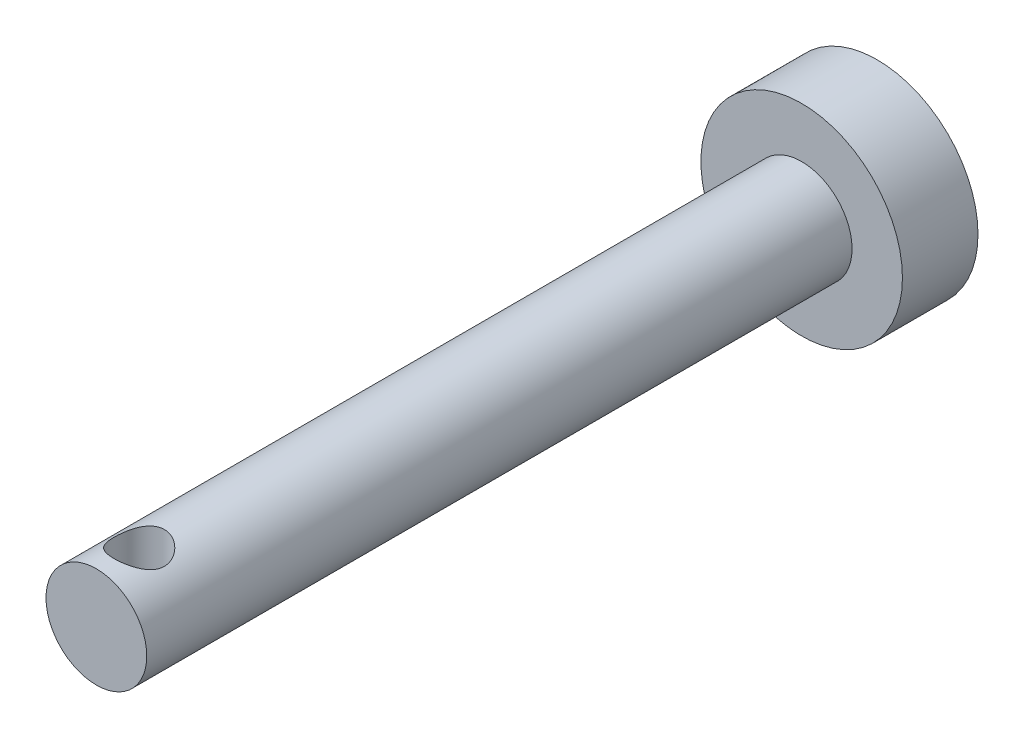
SolidWorks part; units mm, degrees
ref_plane "Front Plane" through (0, 0, 0) normal (0, 0, 1) x (1, 0, 0)
ref_plane "Top Plane" through (0, 0, 0) normal (0, 1, 0) x (1, 0, 0)
ref_plane "Right Plane" through (0, 0, 0) normal (1, 0, 0) x (0, 0, -1)
sketch "Sketch1" plane through (0, 0, 0) normal (1, 0, 0) x (0, 0, -1)
  line L0 (-125, 0) -> (125, 0) construction
  line L1 (125, 4) -> (125, -4) construction
  line L2 (125, 4) -> (122, 4) construction
  line L3 (-125, -2) -> (-125, 2) construction
  point P7 (-125, 0)
  dimension "Length" = 250
  dimension "Head Height" = 3
  dimension "Head Diameter" = 8
  dimension "Diameter" = 4
sketch "Sketch2" plane through (0, 0, 0) normal (1, 0, 0) x (0, 0, -1)
  line L0 (125, 0) -> (125, 4)
  line L1 (125, 4) -> (122, 4)
  line L2 (122, 4) -> (122, 2)
  line L3 (122, 2) -> (-125, 2)
  line L4 (-125, 2) -> (-125, 0)
  line L5 (-125, 0) -> (125, 0)
revolve "Revolve1" add sketch "Sketch2" angle 360 about L0
sketch "Sketch3" plane through (0, 0, 0) normal (1, 0, 0) x (0, 0, -1)
  line L0 (122, 4) -> (122, -4) construction
  line L1 (94, 4.0673) -> (-206, 4.0673)
  line L2 (94, 4.0673) -> (94, -3.766)
  line L3 (94, -3.766) -> (-206, -3.766)
  line L4 (-206, 4.0673) -> (-206, -3.766)
  line L5 (4.4, 0) -> (-4.4, 0) construction
  dimension "D1" = 7.8334
  dimension "D2" = 28
  dimension "D3" = 300
  dimension "D4" = 4.0673
extrude "Cut-Extrude1" cut sketch "Sketch3" against normal through all and the other way through all
sketch "Sketch4" plane through (0, 0, 0) normal (0, 1, 0) x (1, 0, 0)
  line L0 (-4, 122) -> (4, 122) construction
  line L1 (0, -4.4) -> (0, 4.4) construction
  circle A0 centre (0, 95.7) radius 1
  dimension "D1" = 2
  dimension "D2" = 26.3
extrude "Cut-Extrude2" cut sketch "Sketch4" against normal through all and the other way through all
